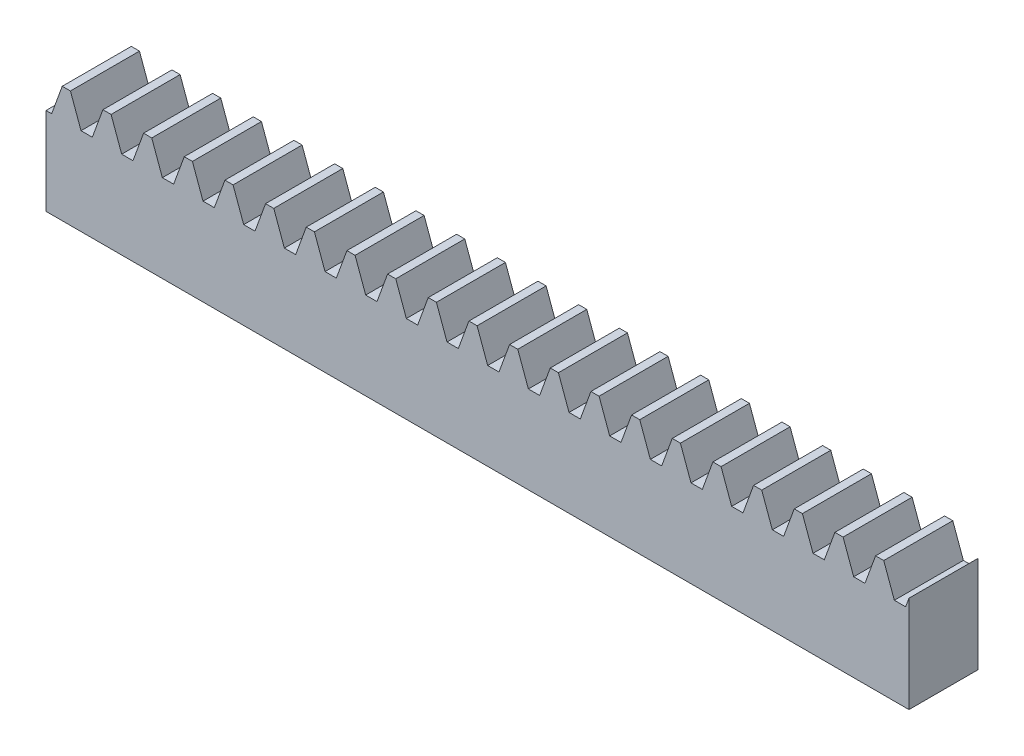
SolidWorks part; units mm, degrees
extrude "Blank" add sketch "BlankSke" against normal blind 8
sketch "BlankSke" plane through (0, 0, 0) normal (0, 0, 1) x (1, 0, 0)
  line L1 (0, 0) -> (100, 0)
  line L2 (0, 0) -> (0, 13.5)
  line L3 (0, 13.5) -> (100, 13.5)
  line L4 (100, 0) -> (100, 13.5)
  dimension "Length" = 100
  dimension "Blank_height" = 13.5
ref_plane "Plane1" through (0, 0, 0) normal (0, 0, 1) x (1, 0, 0)
ref_plane "Plane2" through (0, 0, 0) normal (0, 1, 0) x (1, 0, 0)
ref_plane "Plane3" through (0, 0, 0) normal (1, 0, 0) x (0, 0, -1)
other "Configuration Table"
sketch "HoldingSke" plane through (0, 0, 0) normal (0, 1, 0) x (1, 0, 0)
  line L0 (0, 0) -> (0.0928, 0.6602)
  line L1 (-15, 0) -> (100, 0) construction
  line L2 (0, 0) -> (-2.1039, 2.3779)
  line L3 (0, 0) -> (-11.863, 4.5341)
  line L4 (0, 0) -> (7.9495, 3.3743)
  line L5 (0, 0) -> (-23.7986, -8.8762)
  line L6 (0, 0) -> (-10.5278, -7.1032)
  line L9 (-71.009, 38.7566) -> (22.9603, 72.9586)
  line L10 (-76.2, 3.8779) -> (-64.2, 3.8779)
  line L11 (0, 0) -> (-8, 0)
  line L12 (-76.2, 101.6) -> (-76.147, 101.6)
  line L13 (24.9733, 27.94) -> (52.9518, 28.4284)
  line L14 (24.9733, 27.94) -> (24.9743, 27.94)
  line L15 (24.9733, 27.94) -> (100.4006, 29.5858)
  circle A0 centre (0, 0) radius 19.05
  circle A1 centre (0, 0) radius 6
  circle A2 centre (0, 0) radius 12.7
  dimension "MPH" = 12
  dimension "Diameter" = 38.1
  dimension "Num_teeth" = 23
  dimension "Pitch" = 0.6667
  dimension "Show_teeth" = 998
  dimension "Thickness" = 12.7
  dimension "Ap" = 20
  dimension "Pitch_height" = 12
  dimension "Width" = 8
  dimension "Backlash" = 0.053
  dimension "Addendum_fac" = 1
  dimension "Dedendum_fac" = 1.25
  dimension "Clearance_fac" = 0.25
  dimension "Dedendum_add" = 0.001
  dimension "Length" = 100
  dimension "Module" = 1.5
sketch "TooCutSkeIll" plane through (0, 0, 0) normal (0, 0, 1) x (1, 0, 0)
  line L0 (-1.8687, 13.4605) -> (-0.7447, 10.3724)
  line L1 (-0.3914, 10.125) -> (0.3914, 10.125)
  line L2 (0.7447, 10.3724) -> (1.8687, 13.4605)
  line L3 (100, 13.5) -> (0, 13.5) construction
  line L4 (0, 0) -> (0, 64.897) construction
  line L5 (-13.208, 12) -> (12.954, 12) construction
  line L6 (0, 0) -> (100, 0) construction
  line L7 (1.3371, 12) -> (1.3371, 48.7463) construction
  line L8 (-1.3371, 12) -> (-1.3371, 48.7463) construction
  line L9 (1.9251, 13.5) -> (1.9251, 13.5254)
  line L10 (-1.9251, 13.5) -> (-1.9251, 13.5254)
  line L11 (-1.9251, 13.5254) -> (1.9251, 13.5254)
  arc A0 (0.3914, 10.125) -> (0.7447, 10.3724) centre (0.3914, 10.501) ccw
  arc A1 (-0.7447, 10.3724) -> (-0.3914, 10.125) centre (-0.3914, 10.501) ccw
  arc A2 (1.9251, 13.5) -> (1.8687, 13.4605) centre (1.9251, 13.44) ccw
  arc A3 (-1.8687, 13.4605) -> (-1.9251, 13.5) centre (-1.9251, 13.44) ccw
  dimension "Pitch_height" = 12
  dimension "Addendum_plus" = 1.5254
  dimension "Pressure_angle" = 20
  dimension "Gap_width" = 2.6742
  dimension "Dedendum" = 1.875
extrude "ToothCutIll" [suppressed] cut sketch "TooCutSkeIll" against normal through all
sketch "TooCutSkeSim" plane through (0, 0, 0) normal (0, 0, 1) x (1, 0, 0)
  line L0 (0.6547, 10.125) -> (-0.6547, 10.125)
  line L1 (1.8923, 13.5254) -> (0.6547, 10.125)
  line L2 (0, 17.4625) -> (0, 53.467) construction
  line L3 (1.8923, 13.5254) -> (-1.8923, 13.5254)
  line L6 (-1.8923, 13.5254) -> (-0.6547, 10.125)
  line L9 (-1.3371, 12) -> (1.3371, 12) construction
  line L10 (0, 0) -> (100, 0) construction
  line L11 (1.3371, 12) -> (1.3371, 53.467) construction
  line L12 (-1.3371, 12) -> (-1.3371, 53.467) construction
  dimension "Pitch_height" = 12
  dimension "Addendum_plus" = 1.5254
  dimension "Pressure_angle" = 20
  dimension "Gap_width" = 2.6742
  dimension "Dedendum" = 1.875
extrude "ToothCutSim" cut sketch "TooCutSkeSim" against normal through all
pattern_linear "TeethCuts" count 22 spacing 4.7124 along (1, 0, 0) of "ToothCutIll", "ToothCutSim"
equation "' \"Module@HoldingSke\" = 6.35"
equation "' \"Num_teeth@HoldingSke\" = 12"
equation "' \"Ap@HoldingSke\" =  20"
equation "' \"Ap@HoldingSke\" = 20"
equation "' \"Width@HoldingSke\" = 0.25 * 25.4"
equation "' \"Show_teeth@HoldingSke\" = 500"
equation "' \"Backlash@HoldingSke\" = 0.009 * 25.4"
equation "' \"Addendum_fac@HoldingSke\" = 1.0"
equation "' \"Dedendum_fac@HoldingSke\" = 1.25"
equation "' \"Dedendum_add@HoldingSke\" = 0.00005 * 25.4"
equation "' \"Clearance_fac@HoldingSke\" = 0.25"
equation "' \"Pitch_height@HoldingSke\" = 1 * 25.4"
equation "' \"Length@HoldingSke\" = 4.71 * 25.4"
equation "\"Pitch@HoldingSke\" = 1 / \"Module@HoldingSke\""
equation "\"MPH@HoldingSke\" = \"Dedendum_fac@HoldingSke\" / \"Pitch@HoldingSke\" + 2 * \"Dedendum_add@HoldingSke\" + 0.002 * 25.4"
equation "\"MPH@HoldingSke\" = ((sgn( \"MPH@HoldingSke\" - \"Pitch_height@HoldingSke\")+1)*( \"MPH@HoldingSke\" - \"Pitch_height@HoldingSke\"))/2 + \"Pitch_height@HoldingSke\""
equation "\"Blank_height@BlankSke\" = \"Pitch_height@HoldingSke\" + \"Addendum_fac@HoldingSke\"  / \"Pitch@HoldingSke\" "
equation "\"Length@BlankSke\" =  \"Length@HoldingSke\""
equation "\"Face_width@Blank\" = \"Width@HoldingSke\""
equation "\"Pressure_angle@TooCutSkeIll\" = \"Ap@HoldingSke\""
equation "\"Addendum_plus@TooCutSkeIll\" =  \"Addendum_fac@HoldingSke\"  / \"Pitch@HoldingSke\" + 0.001 *25.4"
equation "\"Dedendum@TooCutSkeIll\" = \"Dedendum_fac@HoldingSke\"  / \"Pitch@HoldingSke\""
equation "\"Pitch_height@TooCutSkeIll\" =  \"MPH@HoldingSke\""
equation "\"Gap_width@TooCutSkeIll\" = 3.14159265 / 2 / \"Pitch@HoldingSke\" + 6 * \"Backlash@HoldingSke\""
equation "\"Pressure_angle@TooCutSkeSim\" = \"Ap@HoldingSke\""
equation "\"Addendum_plus@TooCutSkeSim\" =  \"Addendum_fac@HoldingSke\"  / \"Pitch@HoldingSke\" + 0.001 * 25.4"
equation "\"Dedendum@TooCutSkeSim\" = \"Dedendum_fac@HoldingSke\"  / \"Pitch@HoldingSke\""
equation "\"Pitch_height@TooCutSkeSim\" =  \"MPH@HoldingSke\""
equation "\"Gap_width@TooCutSkeSim\" = 3.14159265 / 2 / \"Pitch@HoldingSke\" + 6 * \"Backlash@HoldingSke\""
equation "\"Root_fillet@TooCutSkeIll\" = \"Clearance_fac@HoldingSke\" / \"Pitch@HoldingSke\" + \"Dedendum_add@HoldingSke\""
equation "\"Break_rad@TooCutSkeIll\" = 0.02 / \"Pitch@HoldingSke\" * 2"
equation "\"Linear_pitch@TeethCuts\" = 3.14159265 / \"Pitch@HoldingSke\""
equation "\"Num_teeth@HoldingSke\" = int( ( \"Length@HoldingSke\" + 0 ) / (3.14159265 / \"Pitch@HoldingSke\")) + 0.9999  + 1"
equation " \"Num_teeth@TeethCuts\" = int( \"Show_teeth@HoldingSke\" ) + 1"
equation " \"Num_teeth@TeethCuts\" = ((sgn( \"Num_teeth@TeethCuts\" - \"Num_teeth@HoldingSke\" )-1)*( \"Num_teeth@TeethCuts\" - \"Num_teeth@HoldingSke\" ))/-2+ \"Num_teeth@HoldingSke\""
equation " \"Num_teeth@TeethCuts\" = ((sgn( \"Num_teeth@TeethCuts\" - 2.0)+1)*( \"Num_teeth@TeethCuts\" - 2.0))/2 +2.0"
